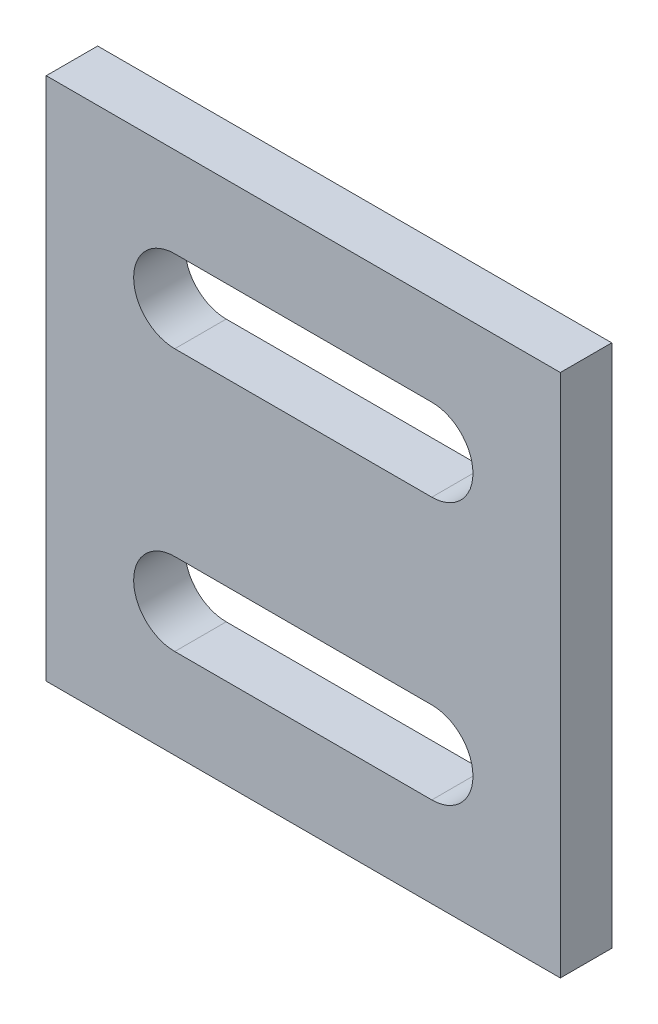
SolidWorks part; units mm, degrees
material "Thornel Mat VMA"
ref_plane "前视基准面" through (0, 0, 0) normal (0, 0, 1) x (1, 0, 0)
ref_plane "上视基准面" through (0, 0, 0) normal (0, 1, 0) x (1, 0, 0)
ref_plane "右视基准面" through (0, 0, 0) normal (1, 0, 0) x (0, 0, -1)
other "Configuration Table"
sketch "草图1" plane through (0, 0, 0) normal (0, 0, 1) x (1, 0, 0)
  line L0 (1.8245, 8.141) -> (-18.1755, 8.141) construction
  line L1 (-18.1755, 18.341) -> (1.8245, 18.341)
  line L2 (-18.1755, 18.341) -> (-18.1755, -2.059)
  line L3 (-18.1755, -2.059) -> (1.8245, -2.059)
  line L4 (1.8245, 18.341) -> (1.8245, -2.059)
  line L5 (-8.1755, 18.341) -> (-8.1755, 8.141) construction
  line L6 (-8.1755, 8.141) -> (-8.1755, -2.059) construction
  line L7 (1.8245, 3.041) -> (-18.1755, 3.041) construction
  line L8 (1.8245, 13.241) -> (-18.1755, 13.241) construction
  line L9 (-13.1755, 13.241) -> (-3.1755, 13.241) construction
  line L10 (-13.1755, 14.841) -> (-3.1755, 14.841)
  line L11 (-13.1755, 11.641) -> (-3.1755, 11.641)
  line L12 (-13.1755, 3.041) -> (-3.1755, 3.041) construction
  line L13 (-13.1755, 1.441) -> (-3.1755, 1.441)
  line L14 (-13.1755, 4.641) -> (-3.1755, 4.641)
  arc A0 (-13.1755, 14.841) -> (-13.1755, 11.641) centre (-13.1755, 13.241) ccw
  arc A1 (-3.1755, 11.641) -> (-3.1755, 14.841) centre (-3.1755, 13.241) ccw
  arc A2 (-13.1755, 1.441) -> (-13.1755, 4.641) centre (-13.1755, 3.041) cw
  arc A3 (-3.1755, 4.641) -> (-3.1755, 1.441) centre (-3.1755, 3.041) cw
  point P13 (-8.1755, 8.141)
  point P16 (-8.1755, 13.241)
  point P23 (-8.1755, 3.041)
  dimension "D4" = 1.6
  dimension "D1" = 10.2
  dimension "D2" = 20
  dimension "D3" = 20.4
  dimension "D5" = 10
extrude "凸台-拉伸1" add sketch "草图1" along normal blind 2 contours L2 L1 L4 L3
